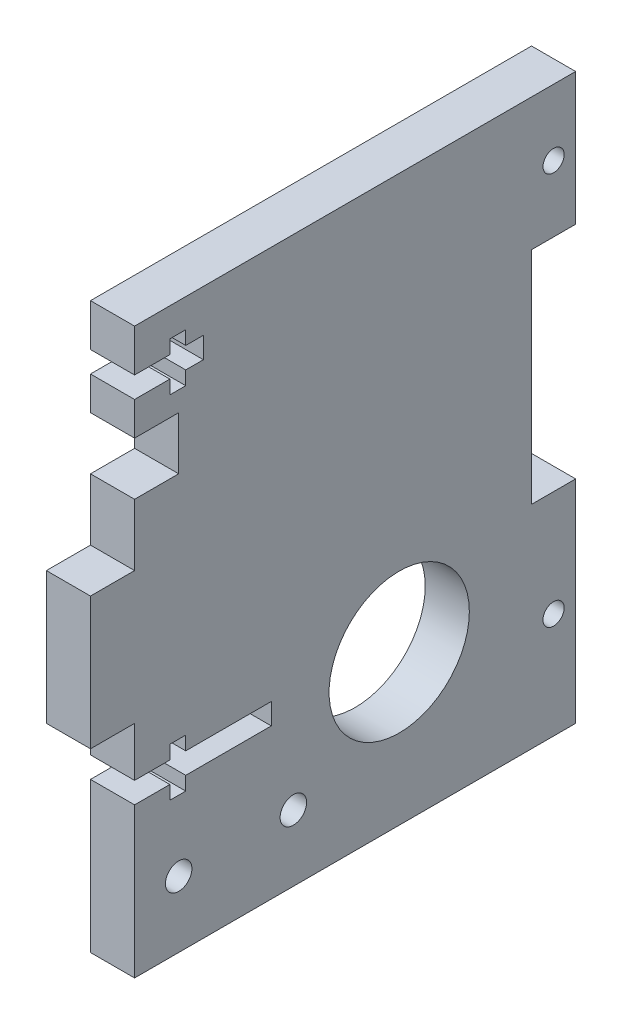
SolidWorks part; units mm, degrees
material "Acrylic (Medium-high impact)"
ref_plane "Front Plane" through (0, 0, 0) normal (0, 0, 1) x (1, 0, 0)
ref_plane "Top Plane" through (0, 0, 0) normal (0, 1, 0) x (1, 0, 0)
ref_plane "Right Plane" through (0, 0, 0) normal (1, 0, 0) x (0, 0, -1)
sketch "Sketch1" plane through (0, 0, 0) normal (1, 0, 0) x (0, 0, -1)
  line L0 (-50, 0) -> (0, 0)
  line L1 (-50, 53) -> (-50, 64)
  line L2 (-50, 25) -> (-50, 0)
  line L3 (-45, 50) -> (-55.472, 50) construction
  line L4 (-20, 64) -> (-20, -5) construction
  line L5 (-42.5, 18.2) -> (-34.5, 18.2) construction
  line L6 (-50, 25) -> (-55, 25)
  line L7 (-55, 25) -> (-55, 40)
  line L8 (-55, 40) -> (-50, 40)
  line L9 (-50, 40) -> (-50, 47)
  line L10 (-50, 47) -> (-45, 47)
  line L11 (-45, 47) -> (-45, 53)
  line L12 (-45, 53) -> (-50, 53)
  line L13 (-42.5, 19.4) -> (-34.5, 19.4)
  line L14 (-42.5, 19.4) -> (-42.5, 17)
  line L15 (-42.5, 17) -> (-34.5, 17)
  line L16 (-34.5, 19.4) -> (-34.5, 17)
  line L17 (-38.5, 19.4) -> (-38.5, 17) construction
  line L18 (-50, 64) -> (0, 64)
  line L19 (0, 64) -> (0, 49)
  line L20 (0, 49) -> (-5, 49)
  line L21 (-5, 49) -> (-5, 24)
  line L22 (-5, 24) -> (0, 24)
  line L23 (0, 24) -> (0, 0)
  circle A0 centre (-20, 17) radius 7.95
  circle A1 centre (-45, 7.5) radius 1.5
  circle A2 centre (-32, 7.5) radius 1.5
  circle A3 centre (-2.5, 56.5) radius 1.2
  circle A4 centre (-2.5, 12) radius 1.2
  point P29 (0, 56.5)
  dimension "D9" = 15.9
  dimension "D10" = 17
  dimension "D15" = 2.4
  dimension "D16" = 7.5
  dimension "D18" = 7.5
  dimension "D17" = 3
  dimension "D21" = 2.4
  dimension "D1" = 25
  dimension "D2" = 15
  dimension "D3" = 10
  dimension "D4" = 6
  dimension "D5" = 11
  dimension "D6" = 50
  dimension "D7" = 25
  dimension "D8" = 15
  dimension "D11" = 8
  dimension "D12" = 5
  dimension "D13" = 5
  dimension "D14" = 5
  dimension "D19" = 6.5
  dimension "D20" = 30
extrude "Boss-Extrude1" add sketch "Sketch1" along normal blind 5
sketch "Sketch2" plane through (5, 0, 0) normal (1, 0, 0) x (0, 0, -1)
  line L0 (-50, 56.8) -> (-46, 56.8)
  line L1 (-50, 64) -> (-50, 53) construction
  line L2 (-46, 56.8) -> (-46, 55.25)
  line L3 (-46, 55.25) -> (-44.2, 55.25)
  line L4 (-44.2, 55.25) -> (-44.2, 56.8)
  line L5 (-44.2, 58) -> (-50, 58) construction
  line L6 (-46, 60.75) -> (-44.2, 60.75)
  line L7 (-46, 59.2) -> (-46, 60.75)
  line L8 (-50, 59.2) -> (-46, 59.2)
  line L9 (-50, 59.2) -> (-50, 56.8)
  line L10 (0, 64) -> (-50, 64) construction
  line L11 (-44.2, 56.8) -> (-42.2, 56.8)
  line L12 (-42.2, 56.8) -> (-42.2, 59.2)
  line L13 (-44.2, 60.75) -> (-44.2, 59.2)
  line L14 (-44.2, 59.2) -> (-42.2, 59.2)
  line L27 (-44.2, 19.4) -> (-42.2, 19.4)
  line L28 (-44.2, 20.95) -> (-44.2, 19.4)
  line L29 (-46, 20.95) -> (-44.2, 20.95)
  line L30 (-46, 19.4) -> (-46, 20.95)
  line L31 (-50, 19.4) -> (-46, 19.4)
  line L32 (-50, 19.4) -> (-50, 17)
  line L33 (-50, 17) -> (-46, 17)
  line L34 (-46, 17) -> (-46, 15.45)
  line L35 (-46, 15.45) -> (-44.2, 15.45)
  line L36 (-44.2, 15.45) -> (-44.2, 17)
  line L37 (-44.2, 17) -> (-42.2, 17)
  line L38 (-42.2, 17) -> (-42.2, 19.4)
  point P19 (-42.2, 58)
  dimension "D1" = 2.4
  dimension "D2" = 5.5
  dimension "D3" = 1.8
  dimension "D4" = 2
  dimension "D5" = 6
  dimension "D6" = 4
  dimension "D7" = 2
extrude "Cut-Extrude1" cut sketch "Sketch2" against normal through all
